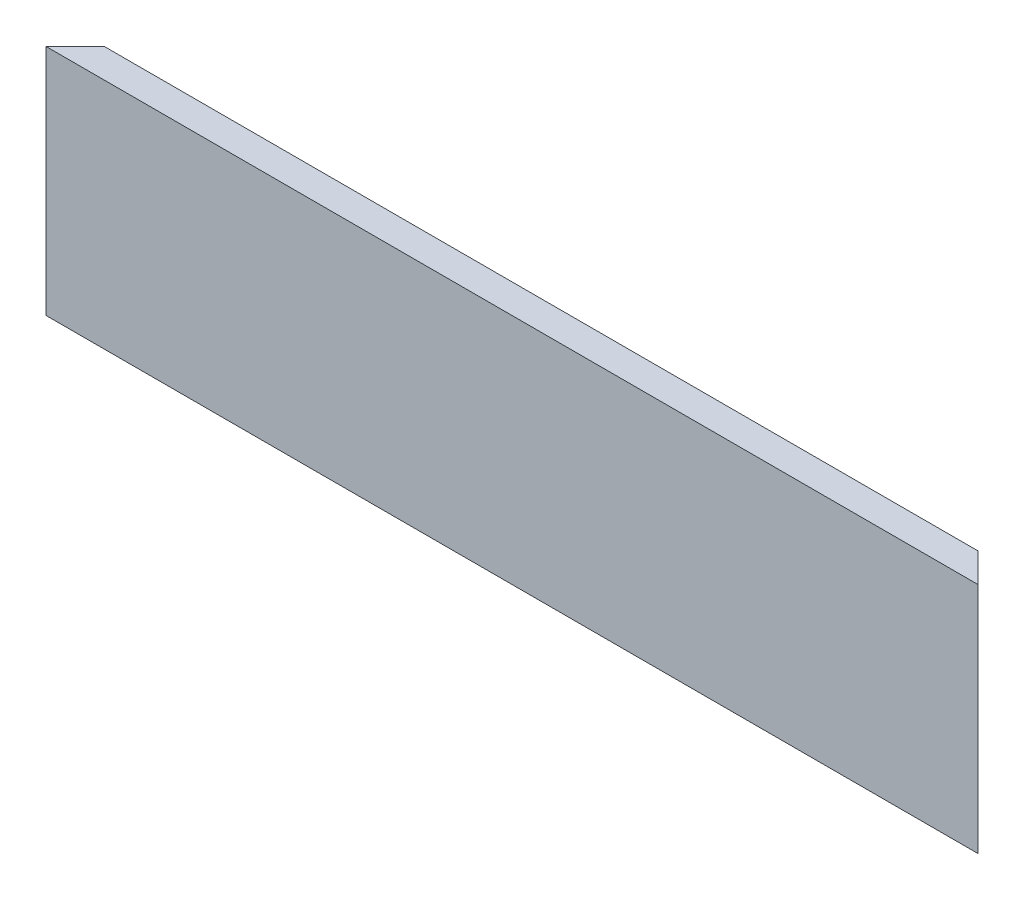
SolidWorks part; units mm, degrees
ref_plane "Front Plane" through (0, 0, 0) normal (0, 0, 1) x (1, 0, 0)
ref_plane "Top Plane" through (0, 0, 0) normal (0, 1, 0) x (1, 0, 0)
ref_plane "Right Plane" through (0, 0, 0) normal (1, 0, 0) x (0, 0, -1)
sketch "Sketch1" plane through (0, 0, 0) normal (1, 0, 0) x (0, 0, -1)
  line L0 (0, 0) -> (0, 25.4)
  line L1 (0, 25.4) -> (3.175, 25.4)
  line L2 (3.175, 25.4) -> (3.175, 3.175)
  line L3 (3.175, 3.175) -> (25.4, 3.175)
  line L4 (25.4, 3.175) -> (25.4, 0)
  line L5 (25.4, 0) -> (0, 0)
  dimension "D1" = 25.4
  dimension "D2" = 3.175
extrude "Boss-Extrude1" add sketch "Sketch1" along normal mid plane 101.6
sketch "Sketch2" plane through (0, 0, 0) normal (0, 1, 0) x (1, 0, 0)
  line L0 (-50.8, 0) -> (-25.4, 25.4)
  line L1 (50.8, 25.4) -> (-50.8, 25.4) construction
  line L2 (-25.4, 25.4) -> (-50.8, 25.4)
  line L3 (-50.8, 25.4) -> (-50.8, 0)
  line L4 (50.8, 0) -> (50.8, 25.4)
  line L5 (50.8, 25.4) -> (25.4, 25.4)
  line L6 (25.4, 25.4) -> (50.8, 0)
  dimension "D1" = 45
  dimension "D2" = 45
extrude "Cut-Extrude1" cut sketch "Sketch2" against normal through all both and the other way through all contours L3 L0 L2 | L6 L4 L5
